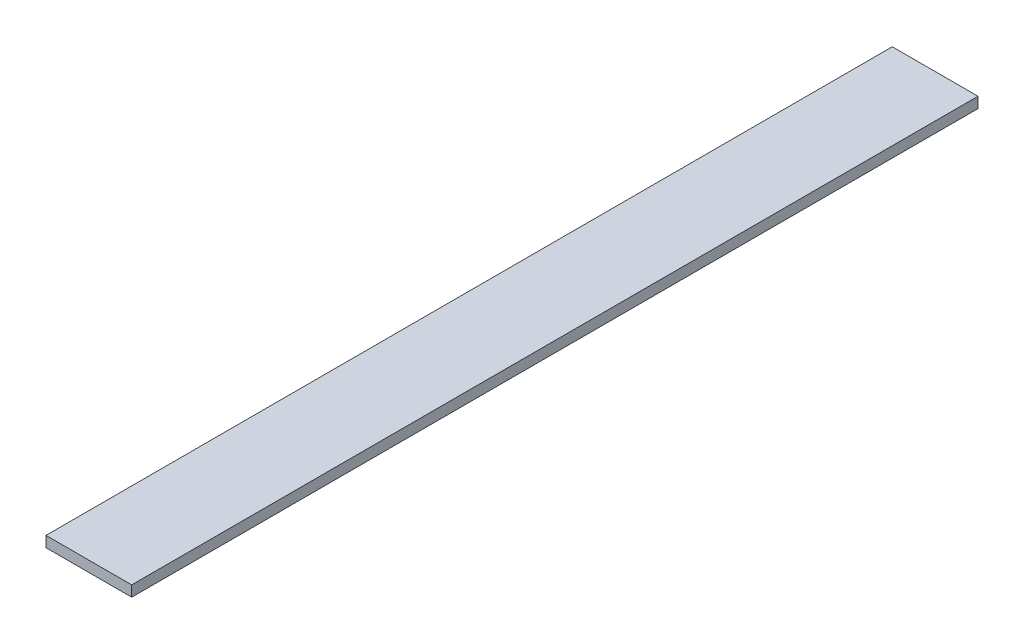
SolidWorks part; units mm, degrees
ref_plane "Front Plane" through (0, 0, 0) normal (0, 0, 1) x (1, 0, 0)
ref_plane "Top Plane" through (0, 0, 0) normal (0, 1, 0) x (1, 0, 0)
ref_plane "Right Plane" through (0, 0, 0) normal (1, 0, 0) x (0, 0, -1)
sketch "Sketch1" plane through (0, 0, 0) normal (0, 1, 0) x (1, 0, 0)
  line L1 (-25.4, -250.825) -> (25.4, -250.825)
  line L2 (-25.4, -250.825) -> (-25.4, 250.825)
  line L3 (-25.4, 250.825) -> (25.4, 250.825)
  line L4 (25.4, -250.825) -> (25.4, 250.825)
  line L5 (-25.4, -250.825) -> (25.4, 250.825) construction
  line L6 (-25.4, 250.825) -> (25.4, -250.825) construction
  point P0 (0, 0)
  dimension "D1" = 501.65
  dimension "D2" = 50.8
extrude "Boss-Extrude1" add sketch "Sketch1" along normal blind 6.35
